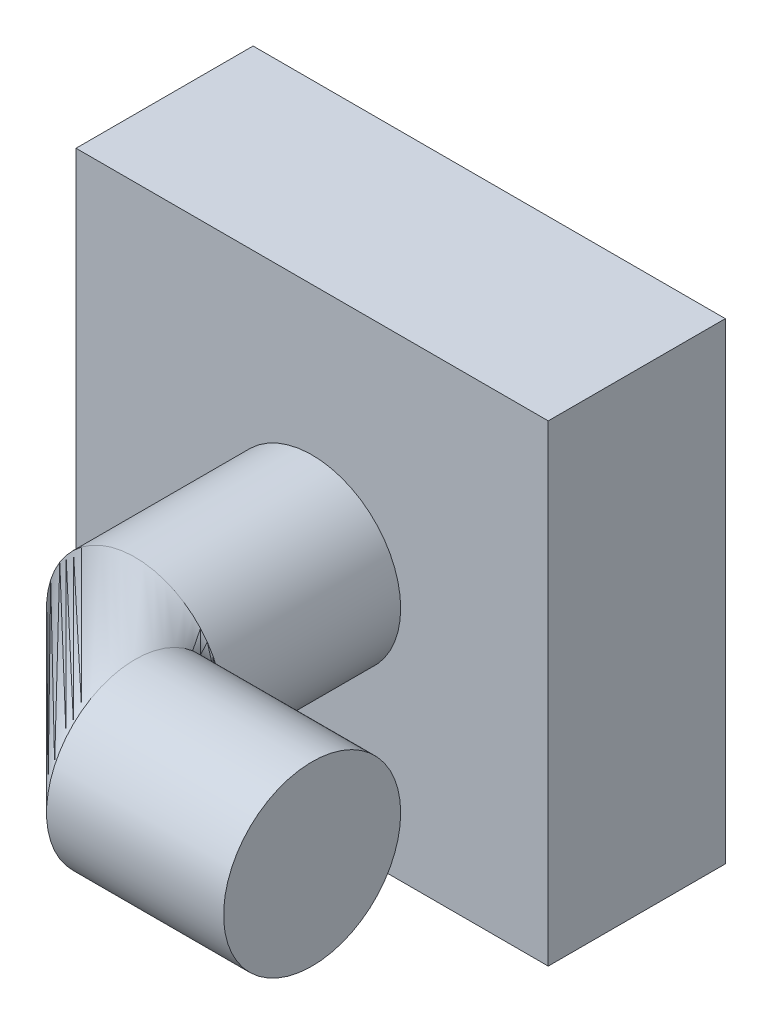
SolidWorks part; units mm, degrees
material "1060 Alloy"
ref_plane "Front Plane" through (0, 0, 0) normal (0, 0, 1) x (1, 0, 0)
ref_plane "Top Plane" through (0, 0, 0) normal (0, 1, 0) x (1, 0, 0)
ref_plane "Right Plane" through (0, 0, 0) normal (1, 0, 0) x (0, 0, -1)
sketch "Sketch1" plane through (0, 0, 0) normal (0, 1, 0) x (1, 0, 0)
  line L0 (57.15, 0) -> (19.05, 0)
  line L1 (0, 19.05) -> (0, 57.15)
  arc A0 (19.05, 0) -> (0, 19.05) centre (19.05, 19.05) cw
  dimension "D1" = 19.05
  dimension "D2" = 38.1
  dimension "D3" = 38.1
  dimension "D4" = 19.05
ref_plane "Plane1" through (57.15, 0, 0) normal (1, 0, 0) x (0, 0, -1)
sketch "Sketch2" plane through (57.15, 0, 0) normal (1, 0, 0) x (0, 0, -1)
  circle A0 centre (0, 0) radius 19.05
  dimension "D1" = 38.1
sweep "Sweep1" add profiles "Sketch2" path "Sketch1"
sketch "Sketch3" plane through (0, 0, -57.15) normal (0, 0, -1) x (-1, 0, 0)
  line L1 (50.8, 50.8) -> (-50.8, 50.8)
  line L2 (50.8, 50.8) -> (50.8, -50.8)
  line L3 (50.8, -50.8) -> (-50.8, -50.8)
  line L4 (-50.8, 50.8) -> (-50.8, -50.8)
  line L5 (50.8, 50.8) -> (-50.8, -50.8) construction
  line L6 (50.8, -50.8) -> (-50.8, 50.8) construction
  point P0 (0, 0)
  dimension "D1" = 101.6
  dimension "D2" = 101.6
extrude "Boss-Extrude1" add sketch "Sketch3" along normal blind 38.1
